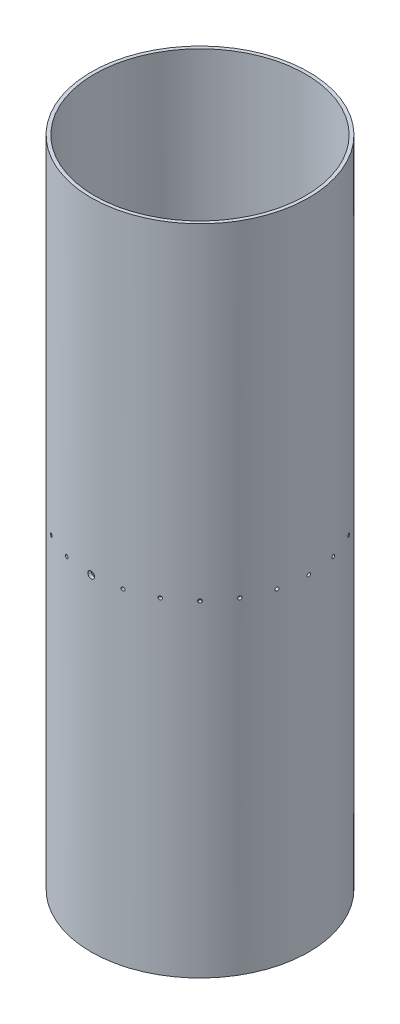
SolidWorks part; units mm, degrees
ref_plane "Front Plane" through (0, 0, 0) normal (0, 0, 1) x (1, 0, 0)
ref_plane "Top Plane" through (0, 0, 0) normal (0, 1, 0) x (1, 0, 0)
ref_plane "Right Plane" through (0, 0, 0) normal (1, 0, 0) x (0, 0, -1)
sketch "Sketch1" plane through (0, 0, 0) normal (0, 1, 0) x (1, 0, 0)
  circle A0 centre (0, 0) radius 101.6
  circle A1 centre (0, 0) radius 98.425
  dimension "D1" = 203.2
  dimension "D2" = 196.85
extrude "Boss-Extrude1" add sketch "Sketch1" along normal blind 609.6
sketch "Sketch2" plane through (0, 0, 0) normal (0, 0, 1) x (1, 0, 0)
  circle A0 centre (0, 304.8) radius 3.175
  dimension "D2" = 6.35
extrude "Cut-Extrude1" cut sketch "Sketch2" against normal through all and the other way through all
sketch "Sketch3" plane through (0, 0, 0) normal (1, 0, 0) x (0, 0, -1)
  circle A0 centre (0, 304.8) radius 1.5875
  dimension "D2" = 3.175
extrude "Cut-Extrude2" cut sketch "Sketch3" against normal blind 609.6
sketch "Sketch4" plane through (0, 0, 0) normal (0, 0, 1) x (1, 0, 0)
  line L0 (0, 0) -> (0, 635.0243) construction
pattern_circular "CirPattern1" count 24 over 360 about axis through (0, 0, 0) along (0, 1, 0) of "Cut-Extrude2"
sketch "Sketch5" plane through (0, 0, 0) normal (0, 0, 1) x (1, 0, 0)
  circle A2 centre (-84.7725, 447.8998) radius 2.125
  dimension "D2" = 4.25
extrude "Cut-Extrude3" cut sketch "Sketch5" against normal through all and the other way through all
